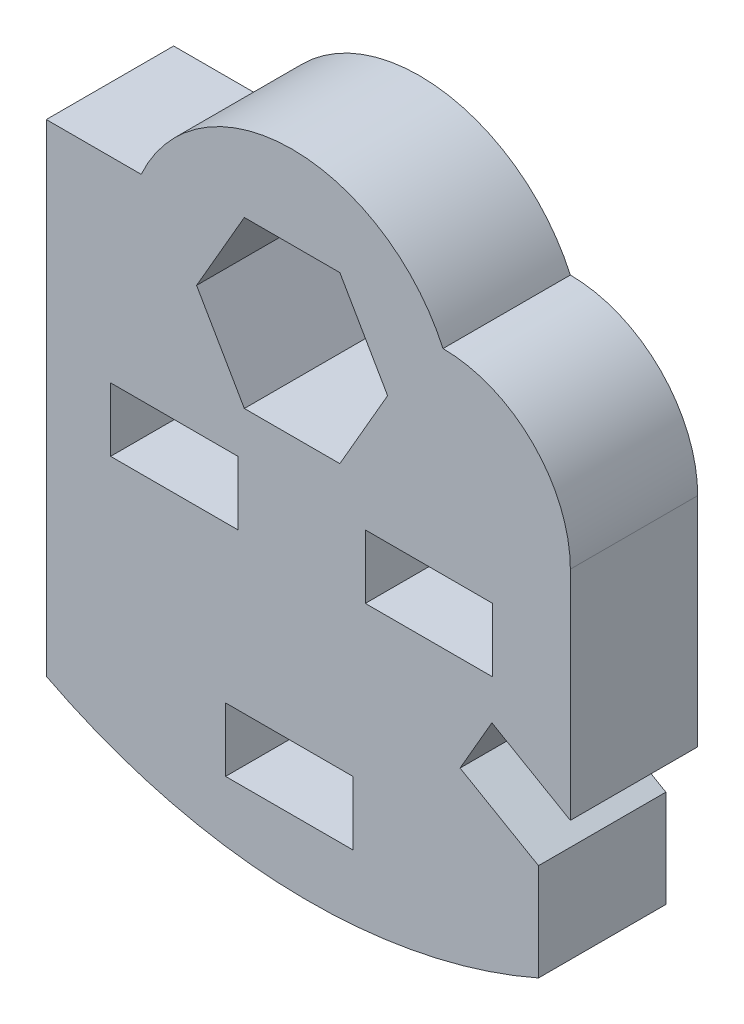
SolidWorks part; units mm, degrees
ref_plane "Front Plane" through (0, 0, 0) normal (0, 0, 1) x (1, 0, 0)
ref_plane "Top Plane" through (0, 0, 0) normal (0, 1, 0) x (1, 0, 0)
ref_plane "Right Plane" through (0, 0, 0) normal (1, 0, 0) x (0, 0, -1)
sketch "Sketch1" plane through (0, 0, 0) normal (0, 0, 1) x (1, 0, 0)
  line L0 (14.4756, 6) -> (15.4756, 7.7321)
  line L1 (3.5, 8.9911) -> (3.5, 10.9911)
  line L2 (7.1111, 2.0911) -> (11.1111, 2.0911)
  line L3 (1.48, 17.1426) -> (1.48, 2)
  line L4 (17.9397, 13.1426) -> (17.9397, 6.3094)
  line L5 (4.4603, 17.1426) -> (1.48, 17.1426)
  line L6 (11.1111, 2.0911) -> (11.1111, 4.0911)
  line L7 (16.9397, 4.5774) -> (16.9397, 1.522)
  line L8 (7.5, 8.9911) -> (7.5, 10.9911)
  line L9 (3.5, 8.9911) -> (7.5, 8.9911)
  line L10 (15.4756, 7.7321) -> (17.9397, 6.3094)
  line L11 (3.5, 10.9911) -> (7.5, 10.9911)
  line L12 (14.4756, 6) -> (16.9397, 4.5774)
  line L13 (11.5, 8.9911) -> (11.5, 10.9911)
  line L14 (11.5, 8.9911) -> (15.5, 8.9911)
  line L15 (15.5, 8.9911) -> (15.5, 10.9911)
  line L16 (11.5, 10.9911) -> (15.5, 10.9911)
  line L17 (7.1111, 2.0911) -> (7.1111, 4.0911)
  line L18 (7.1111, 4.0911) -> (11.1111, 4.0911)
  line L20 (6.2, 14.9911) -> (7.7, 12.393)
  line L21 (7.7, 12.393) -> (10.7, 12.393)
  line L22 (10.7, 12.393) -> (12.2, 14.9911)
  line L23 (12.2, 14.9911) -> (10.7, 17.5892)
  line L24 (10.7, 17.5892) -> (7.7, 17.5892)
  line L25 (7.7, 17.5892) -> (6.2, 14.9911)
  arc A0 (17.9397, 13.1426) -> (13.9397, 17.1426) centre (13.9397, 13.1426) ccw
  arc A1 (1.48, 2) -> (16.9397, 1.522) centre (9.7098, 17.9326) ccw
  arc A3 (13.9397, 17.1426) -> (4.4603, 17.1426) centre (9.2, 14.9926) ccw
  dimension "D1" = 4
  dimension "D2" = 17.9326
  dimension "D9" = 7.7
  dimension "D6" = 4.4603
  dimension "D8" = 7.1111
  dimension "D3" = 5.2045
  dimension "D4" = 1.48
  dimension "D5" = 3.5
  dimension "D7" = 6.2
  dimension "D10" = 9.2
  dimension "D11" = 10.7
  dimension "D12" = 9.7098
  dimension "D13" = 11.5
  dimension "D14" = 14.4756
  dimension "D15" = 15.4756
  dimension "D16" = 1.522
  dimension "D17" = 2.0911
  dimension "D18" = 4.5774
  dimension "D19" = 8.9911
  dimension "D20" = 12.393
  dimension "D21" = 14.9926
extrude "Boss-Extrude1" add sketch "Sketch1" along normal blind 4
